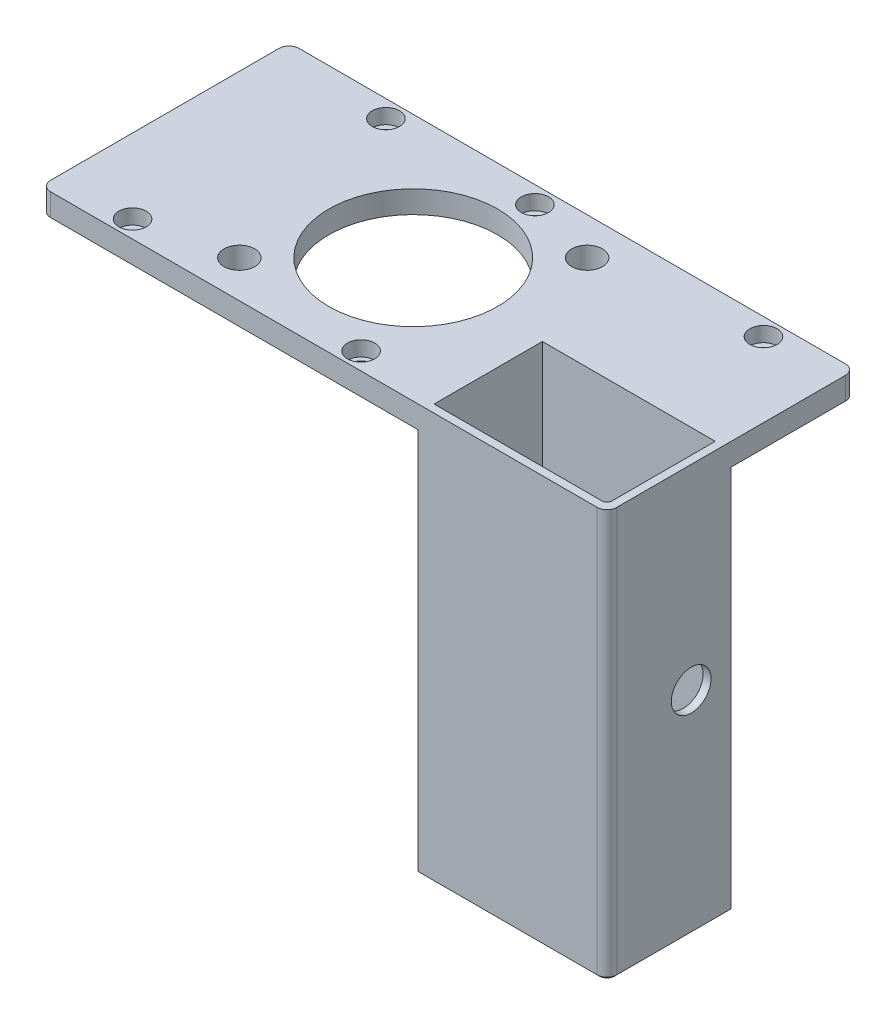
SolidWorks part; units mm, degrees
ref_plane "Alzado" through (0, 0, 0) normal (0, 0, 1) x (1, 0, 0)
ref_plane "Planta" through (0, 0, 0) normal (0, 1, 0) x (1, 0, 0)
ref_plane "Vista lateral" through (0, 0, 0) normal (1, 0, 0) x (0, 0, -1)
sketch "Croquis1" plane through (0, 0, 0) normal (0, 1, 0) x (1, 0, 0)
  line L0 (0, 0) -> (11378.5964, 0) construction
  line L1 (0, 0) -> (0, 11378.5964) construction
  line L2 (-0.1936, 21.5) -> (11378.4028, 21.5) construction
  line L3 (-23, -21.5) -> (23, -21.5) construction
  line L4 (-38, -25) -> (38, -25) construction
  line L5 (-38, -25) -> (-38, 0) construction
  line L6 (-38, 0) -> (38, 0) construction
  line L7 (38, -25) -> (38, 0) construction
  line L8 (-38, -25) -> (38, 0) construction
  line L9 (-38, 0) -> (38, -25) construction
  line L10 (-76, 25) -> (76, 25) construction
  line L11 (0, 0) -> (76, 0) construction
  line L12 (0, 0) -> (0, 25) construction
  line L13 (0, 25) -> (76, 25) construction
  line L14 (76, 0) -> (76, 25) construction
  line L15 (0, 0) -> (76, 25) construction
  line L16 (0, 25) -> (76, 0) construction
  line L17 (0, 0) -> (-76, 0) construction
  line L18 (0, 0) -> (0, 25) construction
  line L19 (0, 25) -> (-76, 25) construction
  line L20 (-76, 0) -> (-76, 25) construction
  line L21 (0, 0) -> (-76, 25) construction
  line L22 (0, 25) -> (-76, 0) construction
  line L23 (76, 25) -> (76, 0)
  line L24 (76, 0) -> (38, 0)
  line L25 (38, 0) -> (38, -25)
  line L26 (38, -25) -> (-38, -25)
  line L27 (-38, -25) -> (-38, 0)
  line L29 (-76, 0) -> (-76, 25) construction
  line L30 (-38, 0) -> (-38, 25)
  line L31 (-38, 25) -> (76, 25)
  circle A0 centre (-15, 21.5) radius 1.6
  circle A1 centre (15, 21.5) radius 1.6
  circle A2 centre (-23, -21.5) radius 1.529
  circle A3 centre (23, -21.5) radius 1.8149
  circle A4 centre (-61, 21.5) radius 1.6 construction
  circle A5 centre (61, 21.5) radius 1.6
  point P13 (0, -12.5)
  point P24 (38, 12.5)
  point P27 (-38, 12.5)
  dimension "D1" = 3.2
  dimension "D2" = 15
  dimension "D3" = 15
  dimension "D4" = 76
  dimension "D5" = 25
  dimension "D6" = 15
  dimension "D7" = 15
  dimension "D8" = 3.5
  dimension "D9" = 3.5
  dimension "D10" = 25
  dimension "D11" = 76
  dimension "D12" = 15
  dimension "D13" = 15
extrude "Saliente-Extruir1" add sketch "Croquis1" along normal blind 4.5
sketch "Croquis2" plane through (0, 4.5, 0) normal (0, 1, 0) x (1, 0, 0)
  line L0 (16, -49.7528) -> (16, 49950.2472) construction
  line L1 (-5.5, 17.5) -> (29.5, 17.5) construction
  line L2 (-5.5, 17.5) -> (-5.5, -17.5) construction
  line L3 (-5.5, -17.5) -> (29.5, -17.5) construction
  line L4 (29.5, 17.5) -> (29.5, -17.5) construction
  line L5 (-5.5, 17.5) -> (29.5, -17.5) construction
  line L6 (-5.5, -17.5) -> (29.5, 17.5) construction
  line L7 (38, -25) -> (38, 0) construction
  line L8 (0, 0) -> (50000, 0) construction
  line L9 (0, 0) -> (0, -50000) construction
  line L10 (38, 0) -> (38, 50000) construction
  line L11 (12, 0) -> (12, -50000) construction
  circle A0 centre (29.5, 17.5) radius 3.1
  circle A1 centre (-5.5, -17.5) radius 3.1
  circle A2 centre (12, 0) radius 17
  point P0 (12, 0)
  dimension "D3" = 6.2
  dimension "D5" = 34
  dimension "D1" = 35
  dimension "D2" = 22
  dimension "D4" = 4
extrude "Cortar-Extruir1" cut sketch "Croquis2" against normal through all
sketch "Croquis3" plane through (0, 4.5, 0) normal (0, 1, 0) x (1, 0, 0)
  circle A0 centre (-15, 21.5) radius 2.75
  circle A1 centre (15, 21.5) radius 2.75
  circle A2 centre (61, 21.5) radius 2.75
  circle A3 centre (23, -21.5) radius 2.75
  circle A4 centre (-23, -21.5) radius 2.75
  dimension "D1" = 5.5
extrude "Cortar-Extruir2" cut sketch "Croquis3" against normal blind 3
sketch "Croquis4" plane through (0, 4.5, 0) normal (0, 1, 0) x (1, 0, 0)
  line L0 (38, -25) -> (38, 0)
  line L1 (38, 0) -> (76, 0)
  line L3 (74.4, -1.6) -> (39.6, -1.6)
  line L6 (76, 0) -> (76, -25)
  line L7 (76, -25) -> (38, -25)
  line L8 (74.4, -1.6) -> (74.4, -23.4)
  line L9 (74.4, -23.4) -> (39.6, -23.4)
  line L10 (39.6, -23.4) -> (39.6, -1.6)
  point P4 (76, 0)
  dimension "D1" = 1.6
  dimension "D2" = 1.6
  dimension "D3" = 1.6
  dimension "D4" = 1.6
extrude "Saliente-Extruir2" add sketch "Croquis4" against normal blind 82
sketch "Croquis5" plane through (0, 0, 1.6) normal (0, 0, 1) x (1, 0, 0)
  line L0 (39.6, -77.5) -> (74.4, -77.5) construction
  circle A0 centre (53.5, -73.5) radius 1.6
  point P6 (0, 0)
  point P7 (53.5, -73.5)
  point P8 (76, -77.5)
  point P12 (92.2953, -3.5675)
  dimension "D1" = 3.2
  dimension "D2" = 4
  dimension "D3" = 22.5
extrude "Cortar-Extruir3" cut sketch "Croquis5" against normal blind 82
sketch "Croquis6" plane through (76, 0, 0) normal (1, 0, 0) x (0, 0, -1)
  circle A0 centre (-8.0496, -34.846) radius 4
  dimension "D1" = 8
extrude "Cortar-Extruir4" cut sketch "Croquis6" against normal up to next
fillet "Redondeo1" radius 2 4 edges at (76, 2.25, -25) (76, -36.5, 25) (-38, 2.25, 25) (-38, 2.25, -25)
fillet "Redondeo2" radius 1 1 edges at (74.4, -36.5, 23.4)
chamfer "Chaflán1" distance 0.5 angle 45 3 edges at (76, -77.5, 11.5) (75.4142, -77.5, 24.4142) (56, -77.5, 25)
